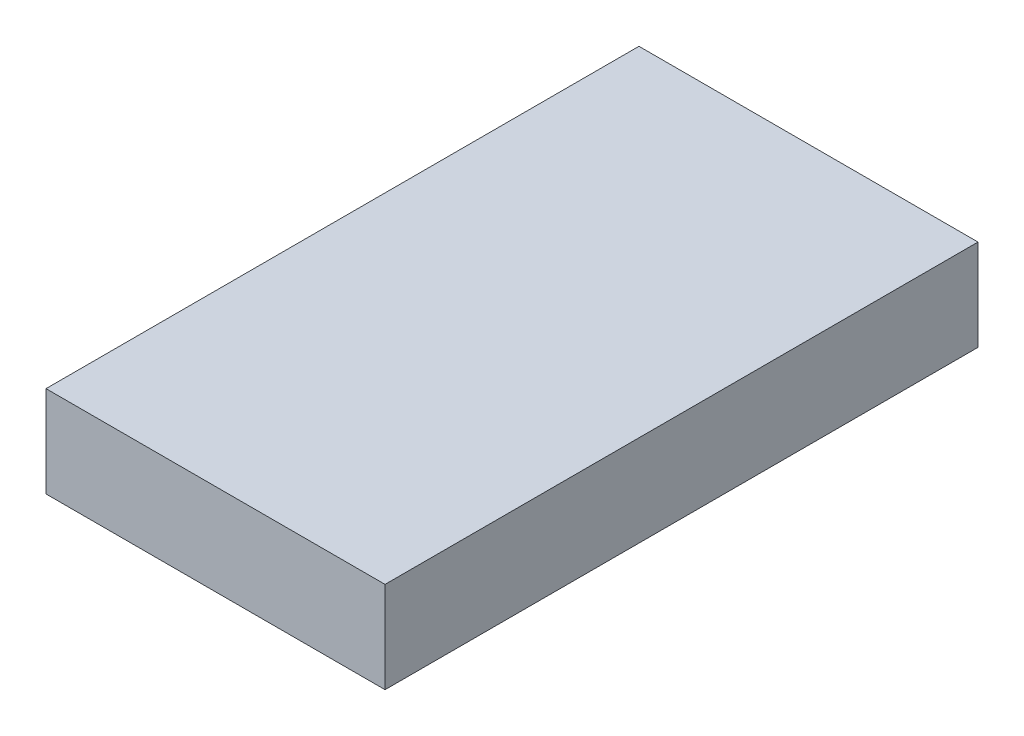
SolidWorks part; units mm, degrees
ref_plane "Front" through (0, 0, 0) normal (0, 0, 1) x (1, 0, 0)
ref_plane "Top" through (0, 0, 0) normal (0, 1, 0) x (1, 0, 0)
ref_plane "Right" through (0, 0, 0) normal (1, 0, 0) x (0, 0, -1)
sketch "草图1" plane through (0, 0, 0) normal (0, 1, 0) x (1, 0, 0)
  line L0 (0, 0) -> (0, -39)
  line L1 (0, 0) -> (22.3, 0)
  line L2 (22.3, 0) -> (22.3, -39)
  line L3 (22.3, -39) -> (0, -39)
extrude "凸台-拉伸1" add sketch "草图1" along normal blind 6
